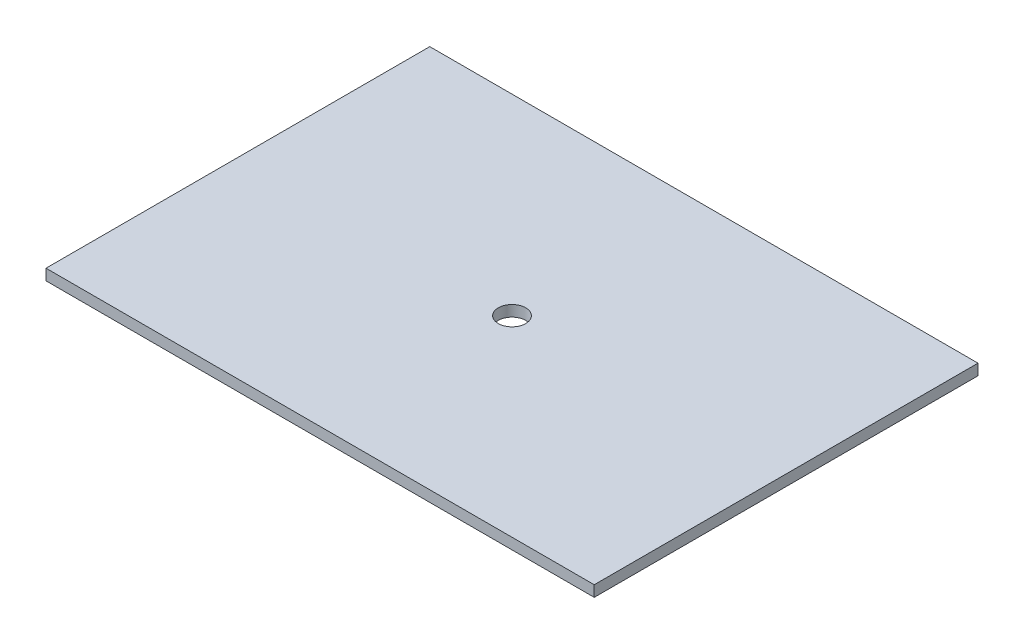
SolidWorks part; units mm, degrees
ref_plane "Front Plane" through (0, 0, 0) normal (0, 0, 1) x (1, 0, 0)
ref_plane "Top Plane" through (0, 0, 0) normal (0, 1, 0) x (1, 0, 0)
ref_plane "Right Plane" through (0, 0, 0) normal (1, 0, 0) x (0, 0, -1)
sketch "Sketch1" plane through (0, 0, 0) normal (0, 1, 0) x (1, 0, 0)
  line L0 (-63.5, 88.9) -> (-63.5, 0) construction
  line L1 (0, 0) -> (-127, 0)
  line L2 (0, 0) -> (0, 88.9)
  line L3 (0, 88.9) -> (-127, 88.9)
  line L4 (-127, 0) -> (-127, 88.9)
  circle A0 centre (-63.5, 44.45) radius 3.175
  dimension "D3" = 6.35
  dimension "D1" = 127
  dimension "D2" = 88.9
extrude "Boss-Extrude1" add sketch "Sketch1" along normal blind 2.54
